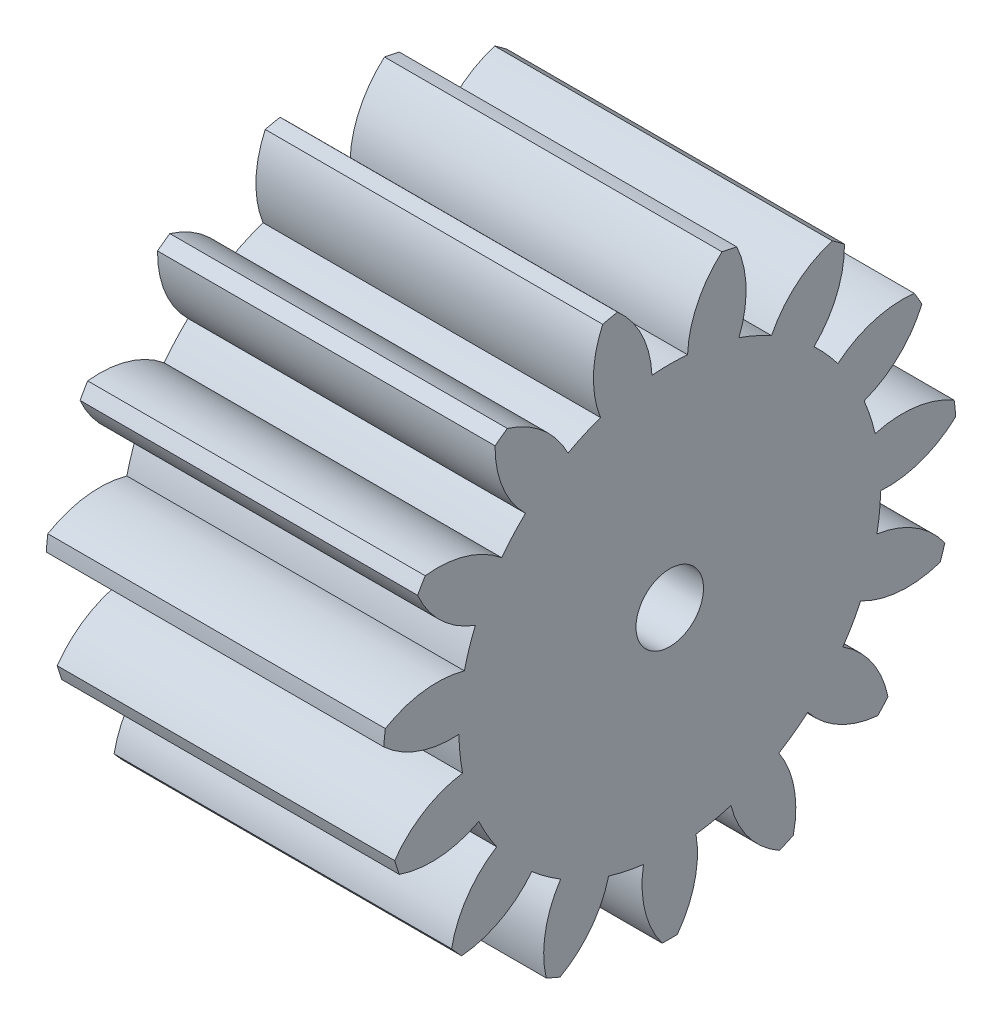
SolidWorks part; units mm, degrees
ref_plane "Plane1" through (0, 0, 0) normal (0, 0, 1) x (1, 0, 0)
ref_plane "Plane2" through (0, 0, 0) normal (0, 1, 0) x (1, 0, 0)
ref_plane "Plane3" through (0, 0, 0) normal (1, 0, 0) x (0, 0, -1)
sketch "HoldingSke" plane through (0, 0, 0) normal (0, 1, 0) x (1, 0, 0)
  line L0 (0, 0) -> (0.644, -0.1725)
  line L1 (-15, 0) -> (100, 0) construction
  line L2 (0, 0) -> (-2.1039, 2.3779)
  line L3 (0, 0) -> (-11.863, 4.5341)
  line L4 (0, 0) -> (8.3417, 2.2352)
  line L5 (0, 0) -> (-46.8476, -17.4728)
  line L6 (0, 0) -> (-12.4344, -8.3896)
  line L7 (-2.1039, 2.3779) -> (8.6586, 51.2059)
  line L8 (-76.2, 54.61) -> (-75.7, 54.61)
  line L9 (-71.009, 38.7566) -> (-53.1078, 45.2721)
  line L10 (-76.2, 71.12) -> (104.1128, 71.12)
  line L11 (0, 0) -> (-15, 0)
  line L12 (-76.2, 101.6) -> (-76.147, 101.6)
  line L13 (24.9733, 27.94) -> (52.9518, 28.4284)
  line L14 (24.9733, 27.94) -> (24.9743, 27.94)
  line L15 (24.9733, 27.94) -> (100.4006, 29.5858)
  line L16 (-63.627, -1.5) -> (-12.827, -1.5)
  circle A0 centre (0, 0) radius 1.5
  circle A1 centre (0, 0) radius 9.374
  circle A2 centre (0, 0) radius 37.5
  circle A3 centre (0, 0) radius 1.5
  dimension "MHD" = 18.748
  dimension "Hub_dia" = 75
  dimension "Bore" = 3
  dimension "MBD" = 3
  dimension "Num_teeth" = 15
  dimension "Pitch_radius" = 180.3128
  dimension "Pitch" = 0.6667
  dimension "Width" = 15
  dimension "Overall_len" = 50
  dimension "Show_teeth" = 15
  dimension "Thickness" = 15
  dimension "OAL" = 50.0001
  dimension "T_dim" = 0.5
  dimension "Ap" = 20
  dimension "H" = 19.05
  dimension "Backlash" = 0.053
  dimension "Addendum_fac" = 1
  dimension "Dedendum_fac" = 1.25
  dimension "Clearance_fac" = 0.25
  dimension "Dedendum_add" = 0.001
  dimension "Module" = 1.5
sketch "BasProSke" plane through (0, 0, 0) normal (0, 1, 0) x (1, 0, 0)
  line L0 (-10, 0) -> (60, 0) construction
  line L1 (0, 0) -> (0, 12.75)
  line L2 (0, 0) -> (15, 0)
  line L3 (15, 0) -> (15, 12.75)
  line L4 (15, 12.75) -> (0, 12.75)
  dimension "Diameter" = 25.5
  dimension "Thickness" = 15
revolve "Base-Revolve" add sketch "BasProSke" angle 360 about L0
sketch "TooCutSke" plane through (0, 0, 0) normal (1, 0, 0) x (0, 0, -1)
  line L1 (0, 0) -> (0, 107) construction
  line L2 (0, 0) -> (-1.2686, 11.1782) construction
  line L3 (0, 0) -> (-4.6563, 21.9061) construction
  line L4 (-1.2686, 11.1782) -> (-2.3281, 10.953) construction
  arc A0 (0.7915, 9.3405) -> (-0.7915, 9.3405) centre (0, 0) ccw
  arc A1 (2.3447, 12.5584) -> (-2.3447, 12.5584) centre (0, 0) ccw
  circle A2 centre (0, 0) radius 11.25 construction
  circle A3 centre (0, 0) radius 10.5715 construction
  arc A4 (-0.7915, 9.3405) -> (-2.3447, 12.5584) centre (-5.2877, 9.1541) ccw
  arc A5 (2.3447, 12.5584) -> (0.7915, 9.3405) centre (5.2877, 9.1541) ccw
  dimension "Root_dia" = 18.748
  dimension "Overcut_dia" = 25.5508
  dimension "Pitch_dia" = 22.5
  dimension "Base_dia" = 21.1431
  dimension "Flank_rad" = 4.5
  dimension "Half_ang" = 12
  dimension "Half_CT" = 1.0832
extrude "ToothCut" cut sketch "TooCutSke" along normal through all
fillet "Breaks" [suppressed] radius 0.03
fillet "RootFillets" [suppressed] radius 0.376
pattern_circular "TeethCuts" count 15 every 24 about axis through (-10, 0, 0) along (1, 0, 0) of "ToothCut", "RootFillets", "Breaks"
sketch "HubNeaOneSke" plane through (0, 0, 0) normal (-1, 0, 0) x (0, 0, 1)
  circle A0 centre (0, 0) radius 9.374
  dimension "Diameter" = 18.748
extrude "HubNearOne" [suppressed] add sketch "HubNeaOneSke" along normal blind 35.0001
sketch "HubNeaBotSke" plane through (0, 0, 0) normal (-1, 0, 0) x (0, 0, 1)
  circle A0 centre (0, 0) radius 9.374
  dimension "Diameter" = 18.748
extrude "HubNearBoth" [suppressed] add sketch "HubNeaBotSke" along normal blind 17.5
ref_plane "FarPln" through (15, 0, 0) normal (1, 0, 0) x (0, 0, -1)
sketch "HubFarSke" plane through (15, 0, 0) normal (1, 0, 0) x (0, 0, -1)
  circle A0 centre (0, 0) radius 9.374
  dimension "Diameter" = 18.748
extrude "HubFar" [suppressed] add sketch "HubFarSke" along normal blind 17.5
sketch "BorSke" plane through (0, 0, 0) normal (1, 0, 0) x (0, 0, -1)
  circle A0 centre (0, 0) radius 1.5
  dimension "Diameter" = 3
extrude "Bore" cut sketch "BorSke" along normal mid plane 100.0001
sketch "KeySke" plane through (0, 0, 0) normal (1, 0, 0) x (0, 0, -1)
  line L0 (-0.6, 0) -> (-0.6, 2)
  line L1 (-0.6, 2) -> (0.6, 2)
  line L2 (0.6, 2) -> (0.6, 0)
  line L3 (0, 0) -> (0, 34) construction
  line L4 (-0.6, 0) -> (0.6, 0)
  dimension "Offset" = 2
  dimension "Width" = 1.2
extrude "Keyway" [suppressed] cut sketch "KeySke" along normal mid plane 100.0001
pattern_circular "Keyway2" [suppressed] count 2 every 90 about axis through (-10, 0, 0) along (1, 0, 0)
equation "' \"Module@HoldingSke\" = 6.35"
equation "' \"Num_teeth@HoldingSke\" = 12"
equation "' \"Ap@HoldingSke\" =  20"
equation "' \"Width@HoldingSke\" = 0.5 * 25.4"
equation "' \"Hub_dia@HoldingSke\"= 1 * 25.4"
equation "' \"Overall_len@HoldingSke\" = 1.0 * 25.4"
equation "' \"Bore@HoldingSke\" = 0.75 * 25.4"
equation "' \"T_dim@HoldingSke\" = 0.1 * 25.4"
equation "' \"Width@KeySke\" = 0.25 * 25.4"
equation "' \"Show_teeth@HoldingSke\" = 13"
equation "' \"Backlash@HoldingSke\" = 0.009 * 25.4"
equation "' \"Addendum_fac@HoldingSke\" = 1.0"
equation "' \"Dedendum_fac@HoldingSke\" = 1.25"
equation "' \"Dedendum_add@HoldingSke\" = 0.00005 * 25.4"
equation "' \"Clearance_fac@HoldingSke\" = 0.25"
equation "\"Pitch@HoldingSke\" = 1 / \"Module@HoldingSke\""
equation "\"Overcut_dia@TooCutSke\" = (\"Num_teeth@HoldingSke\" + 2 * \"Addendum_fac@HoldingSke\") / \"Pitch@HoldingSke\" + 0.002 * 25.4"
equation "\"Pitch_dia@TooCutSke\" = \"Num_teeth@HoldingSke\" / \"Pitch@HoldingSke\""
equation "\"Base_dia@TooCutSke\" = \"Num_teeth@HoldingSke\" / \"Pitch@HoldingSke\" * cos((\"Ap@HoldingSke\"  * 3.14159265 / 180))"
equation "\"Root_dia@TooCutSke\" = (\"Num_teeth@HoldingSke\" + 2) / \"Pitch@HoldingSke\" - 2 * (\"Addendum_fac@HoldingSke\" + \"Dedendum_fac@HoldingSke\") / \"Pitch@HoldingSke\" - \"Dedendum_add@HoldingSke\" * 2"
equation "\"Half_ang@TooCutSke\" = 180 / \"Num_teeth@HoldingSke\""
equation "\"Half_CT@TooCutSke\" = \"Num_teeth@HoldingSke\" / \"Pitch@HoldingSke\" * sin((3.14159265 / 2 / \"Num_teeth@HoldingSke\")) / 2 - 7 * \"Backlash@HoldingSke\" / 4"
equation "\"Flank_rad@TooCutSke\" = \"Num_teeth@HoldingSke\" / \"Pitch@HoldingSke\" / 5"
equation "\"Radius@RootFillets\" = \"Clearance_fac@HoldingSke\" / \"Pitch@HoldingSke\" + \"Dedendum_add@HoldingSke\""
equation "\"Break_rad@Breaks\" = 0.02 / \"Pitch@HoldingSke\""
equation "\"Thickness@HoldingSke\" = \"Width@HoldingSke\""
equation "\"OAL@HoldingSke\" = \"Thickness@HoldingSke\""
equation "\"MHD@HoldingSke\" = (\"Num_teeth@HoldingSke\" + 2) / \"Pitch@HoldingSke\" - 2 * (\"Addendum_fac@HoldingSke\" + \"Dedendum_fac@HoldingSke\")  / \"Pitch@HoldingSke\" - \"Dedendum_add@HoldingSke\" * 2"
equation "\"MBD@HoldingSke\" = (\"Num_teeth@HoldingSke\" + 2) / \"Pitch@HoldingSke\" - 2 * (\"Addendum_fac@HoldingSke\" + \"Dedendum_fac@HoldingSke\")  / \"Pitch@HoldingSke\" - \"Dedendum_add@HoldingSke\" * 2 - 0.002 * 25.4"
equation "\"MHD@HoldingSke\" = ((sgn( \"MHD@HoldingSke\" - \"Hub_dia@HoldingSke\" )-1)*( \"MHD@HoldingSke\" - \"Hub_dia@HoldingSke\" ))/-2+ \"Hub_dia@HoldingSke\""
equation "\"MBD@HoldingSke\" = ((sgn( \"MBD@HoldingSke\" - \"Bore@HoldingSke\" )-1)*( \"MBD@HoldingSke\" - \"Bore@HoldingSke\" ))/-2+ \"Bore@HoldingSke\""
equation "\"OAL@HoldingSke\" = ((sgn( \"OAL@HoldingSke\" - \"Overall_len@HoldingSke\" )+1)*( \"OAL@HoldingSke\" - \"Overall_len@HoldingSke\" ))/2 + \"Overall_len@HoldingSke\" + 0.000002 * 25.4"
equation "\"Num_teeth@TeethCuts\" = int( \"Show_teeth@HoldingSke\" ) + 1"
equation "\"Num_teeth@TeethCuts\" = ((sgn( \"Num_teeth@TeethCuts\" - \"Num_teeth@HoldingSke\" )-1)*( \"Num_teeth@TeethCuts\" - \"Num_teeth@HoldingSke\" ))/-2+ \"Num_teeth@HoldingSke\""
equation "\"Num_teeth@TeethCuts\" = ((sgn( \"Num_teeth@TeethCuts\" - 2.0)+1)*( \"Num_teeth@TeethCuts\" - 2.0))/2 +2.0"
equation "\"Angle@TeethCuts\" = 360.0 / \"Num_teeth@HoldingSke\""
equation "\"Diameter@BasProSke\" = (\"Num_teeth@HoldingSke\" + 2 * \"Addendum_fac@HoldingSke\") / \"Pitch@HoldingSke\""
equation "\"Thickness@BasProSke\"  = \"Thickness@HoldingSke\""
equation "' \"Fillet_rad@BasProSke\" =  \"Thickness@HoldingSke\" * 0.05"
equation "\"MHD@HoldingSke\" = ((sgn( \"MHD@HoldingSke\" - \"Root_dia@TooCutSke\" )-1)*( \"MHD@HoldingSke\" - \"Root_dia@TooCutSke\" ))/-2+ \"Root_dia@TooCutSke\""
equation "\"Diameter@HubNeaOneSke\" = \"MHD@HoldingSke\""
equation "\"Length@HubNearOne\" = \"OAL@HoldingSke\" - \"Thickness@BasProSke\""
equation "\"Diameter@HubNeaBotSke\" = \"MHD@HoldingSke\""
equation "\"Length@HubNearBoth\" = ( \"OAL@HoldingSke\" - \"Thickness@BasProSke\" ) / 2.0"
equation "\"Thickness@FarPln\" = \"Thickness@BasProSke\""
equation "\"Diameter@HubFarSke\" = \"MHD@HoldingSke\""
equation "\"Length@HubFar\" = ( \"OAL@HoldingSke\" - \"Thickness@BasProSke\" ) / 2.0"
equation "\"Diameter@BorSke\" = \"MBD@HoldingSke\""
equation "\"D1@Bore\" = \"OAL@HoldingSke\" * 2.0"
equation "\"D1@Keyway\" = \"OAL@HoldingSke\" * 2.0"
equation "\"Offset@KeySke\" = \"T_dim@HoldingSke\" + \"MBD@HoldingSke\" / 2.0"
